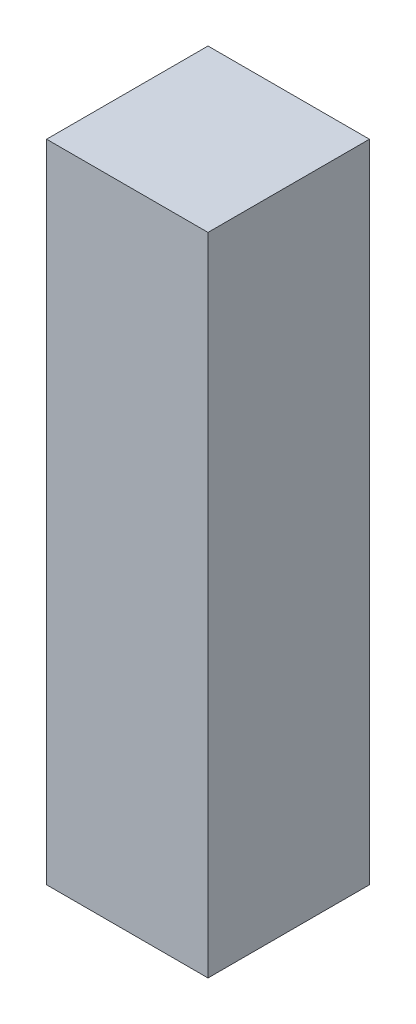
SolidWorks part; units mm, degrees
ref_plane "Front Plane" through (0, 0, 0) normal (0, 0, 1) x (1, 0, 0)
ref_plane "Top Plane" through (0, 0, 0) normal (0, 1, 0) x (1, 0, 0)
ref_plane "Right Plane" through (0, 0, 0) normal (1, 0, 0) x (0, 0, -1)
sketch "Sketch1" plane through (0, 0, 0) normal (0, 1, 0) x (1, 0, 0)
  line L1 (-1.25, -1.25) -> (1.25, -1.25)
  line L2 (-1.25, -1.25) -> (-1.25, 1.25)
  line L3 (-1.25, 1.25) -> (1.25, 1.25)
  line L4 (1.25, -1.25) -> (1.25, 1.25)
  line L5 (-1.25, -1.25) -> (1.25, 1.25) construction
  line L6 (-1.25, 1.25) -> (1.25, -1.25) construction
  point P0 (0, 0)
  dimension "D1" = 2.5
extrude "Boss-Extrude1" add sketch "Sketch1" along normal blind 10
